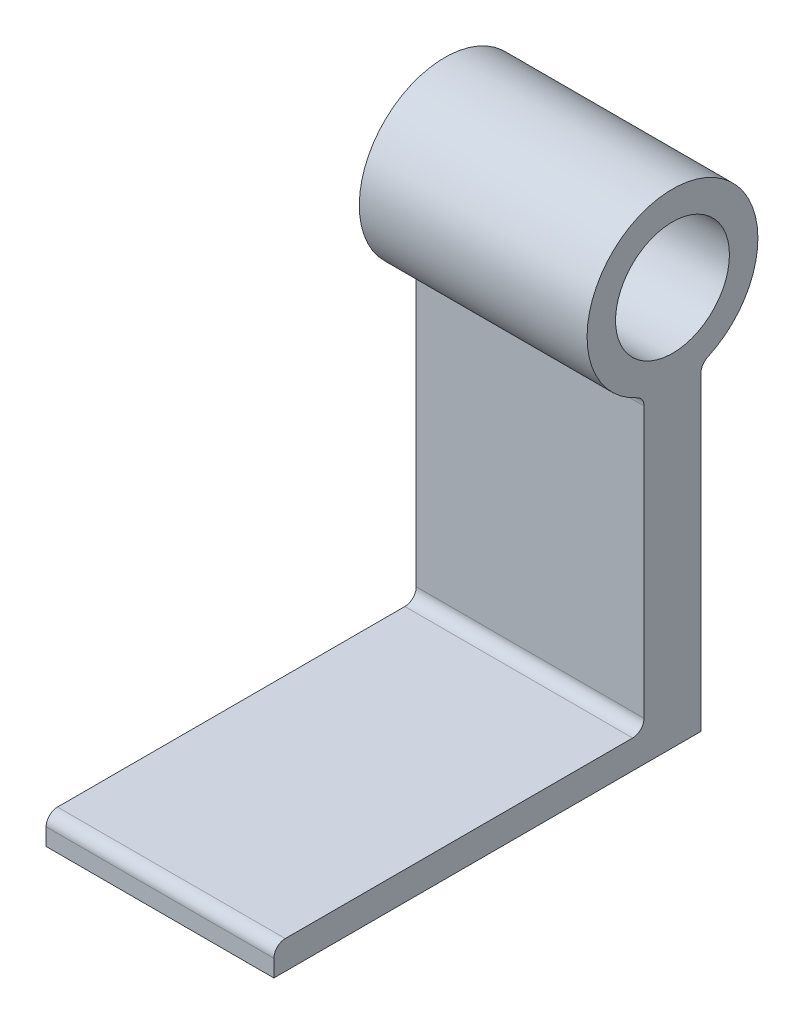
SolidWorks part; units mm, degrees
material "ABS"
ref_plane "Front Plane" through (0, 0, 0) normal (0, 0, 1) x (1, 0, 0)
ref_plane "Top Plane" through (0, 0, 0) normal (0, 1, 0) x (1, 0, 0)
ref_plane "Right Plane" through (0, 0, 0) normal (1, 0, 0) x (0, 0, -1)
sketch "Sketch1" plane through (0, 0, 0) normal (1, 0, 0) x (0, 0, -1)
  line L0 (0, 0) -> (-95.25, 0)
  line L1 (-95.25, 0) -> (-95.25, 6.35)
  line L2 (-95.25, 6.35) -> (-12.7, 6.35)
  line L3 (-12.7, 6.35) -> (-12.7, 70.9395)
  line L4 (-12.7, 70.9395) -> (0, 70.9395)
  line L5 (0, 70.9395) -> (0, 0)
  circle A0 centre (-6.35, 88.9) radius 19.05
  circle A1 centre (-6.35, 88.9) radius 12.7
  dimension "D1" = 38.1
  dimension "D7" = 25.4
  dimension "D2" = 19.05
  dimension "D3" = 12.7
  dimension "D4" = 88.9
  dimension "D5" = 88.9
  dimension "D6" = 6.35
extrude "Boss-Extrude1" add sketch "Sketch1" along normal blind 50.8 contours A0 L3 L2 L1 L0 L5 | L4 A0 A1 | L4 A0
fillet "Fillet1" radius 2.54 3 edges at (25.4, 6.35, 12.7) (25.4, 70.9395, 0) (25.4, 70.9395, 12.7)
fillet "Fillet2" radius 2.54 1 edges at (25.4, 6.35, 95.25)
